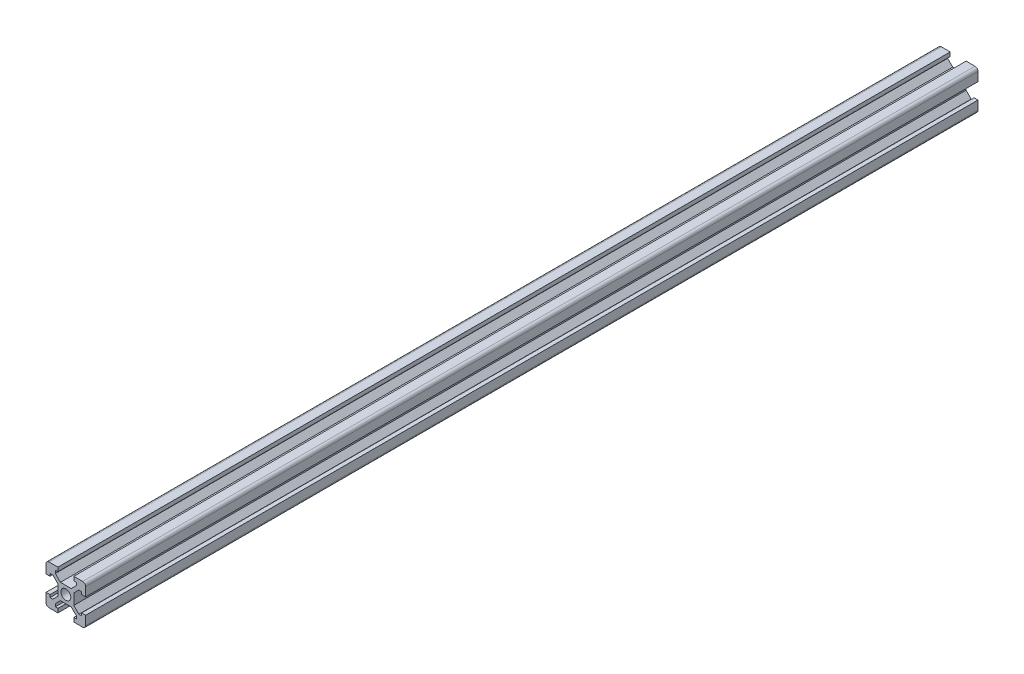
SolidWorks part; units mm, degrees
material "1060 Сплав"
ref_plane "Top" through (0, 0, 0) normal (0, 0, 1) x (1, 0, 0)
ref_plane "Сверху" through (0, 0, 0) normal (0, 1, 0) x (1, 0, 0)
ref_plane "Справа" through (0, 0, 0) normal (1, 0, 0) x (0, 0, -1)
sketch "Эскиз1" plane through (0, 0, 0) normal (0, 0, 1) x (1, 0, 0)
  line L0 (14, 20) -> (20, 20)
  line L1 (0, 0) -> (6, 0)
  line L2 (0, 0) -> (0, 6)
  line L3 (0, 20) -> (6, 20)
  line L4 (20, 0) -> (20, 6)
  line L5 (0, 14) -> (0, 20)
  line L6 (14, 0) -> (20, 0)
  line L7 (20, 14) -> (20, 20)
  line L8 (0, 0) -> (35355.3391, 35355.3391) construction
  line L9 (0, 20) -> (35355.3391, -35335.3391) construction
  line L22 (0, 14) -> (2, 14)
  line L23 (2, 14) -> (2, 15.3)
  line L24 (2, 15.3) -> (3.4272, 15.3)
  line L25 (3.4272, 15.3) -> (6, 12.7272)
  line L26 (6, 12.7272) -> (6, 7.2728)
  line L27 (6, 7.2728) -> (3.4272, 4.7)
  line L28 (3.4272, 4.7) -> (2, 4.7)
  line L29 (2, 4.7) -> (2, 6)
  line L30 (2, 6) -> (0, 6)
  line L31 (6, 0) -> (6, 2)
  line L32 (6, 2) -> (4.7, 2)
  line L33 (4.7, 2) -> (4.7, 3.4272)
  line L34 (4.7, 3.4272) -> (7.2728, 6)
  line L35 (7.2728, 6) -> (12.684, 6)
  line L36 (12.684, 6) -> (15.3, 3.4272)
  line L37 (15.3, 3.4272) -> (15.3, 2)
  line L38 (15.3, 2) -> (14, 2)
  line L39 (14, 2) -> (14, 0)
  line L40 (20, 6) -> (18, 6)
  line L41 (18, 6) -> (18, 4.7)
  line L42 (18, 4.7) -> (16.5728, 4.7)
  line L43 (16.5728, 4.7) -> (14, 7.2728)
  line L44 (14, 7.2728) -> (14, 12.7272)
  line L45 (14, 12.7272) -> (16.5728, 15.3)
  line L46 (16.5728, 15.3) -> (18, 15.3)
  line L47 (18, 15.3) -> (18, 14)
  line L48 (18, 14) -> (20, 14)
  line L49 (6, 20) -> (6, 18)
  line L50 (6, 18) -> (4.7, 18)
  line L51 (4.7, 18) -> (4.7, 16.5728)
  line L52 (4.7, 16.5728) -> (7.2728, 14)
  line L53 (7.2728, 14) -> (12.7272, 14)
  line L54 (12.7272, 14) -> (15.3, 16.5728)
  line L55 (15.3, 16.5728) -> (15.3, 18)
  line L56 (15.3, 18) -> (14, 18)
  line L57 (14, 18) -> (14, 20)
  circle A0 centre (10, 10) radius 2.5
extrude "Бобышка-Вытянуть1" add sketch "Эскиз1" along normal blind 450
fillet "Скругление1" radius 1.5 4 edges at (0, 20, 225) (20, 20, 225) (20, 0, 225) (0, 0, 225)
